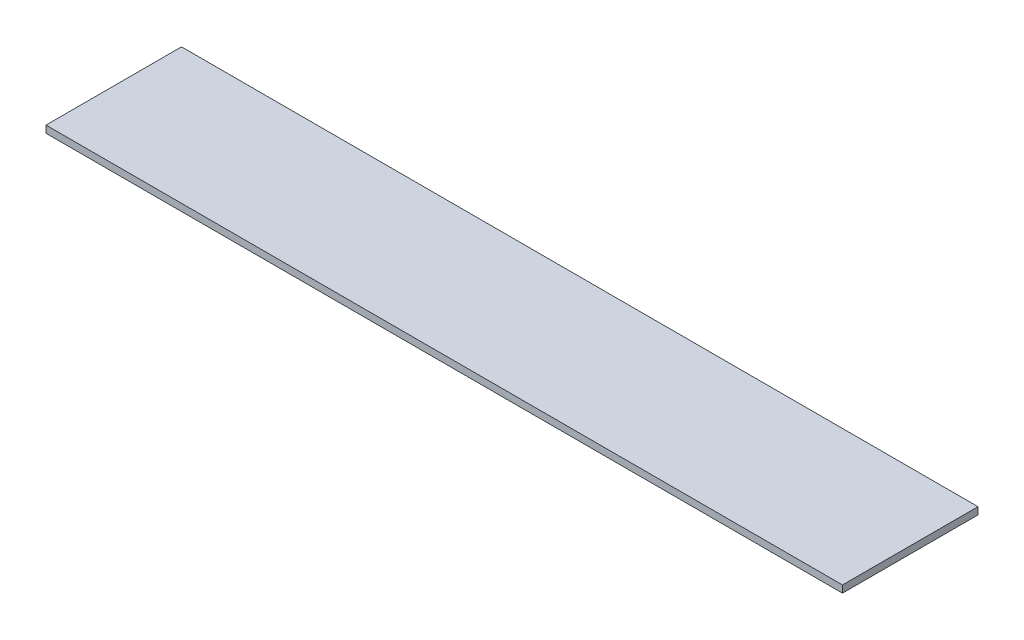
SolidWorks part; units mm, degrees
material "Pino"
ref_plane "Alzado" through (0, 0, 0) normal (0, 0, 1) x (1, 0, 0)
ref_plane "Planta" through (0, 0, 0) normal (0, 1, 0) x (1, 0, 0)
ref_plane "Vista lateral" through (0, 0, 0) normal (1, 0, 0) x (0, 0, -1)
sketch "Sketch1" plane through (0, 0, 0) normal (0, 1, 0) x (1, 0, 0)
  line L1 (-167.5, -28.5) -> (167.5, -28.5)
  line L2 (-167.5, -28.5) -> (-167.5, 28.5)
  line L3 (-167.5, 28.5) -> (167.5, 28.5)
  line L4 (167.5, -28.5) -> (167.5, 28.5)
  line L5 (-167.5, -28.5) -> (167.5, 28.5) construction
  line L6 (-167.5, 28.5) -> (167.5, -28.5) construction
  point P0 (0, 0)
  dimension "D1" = 335
  dimension "D2" = 57
extrude "Extrude1" add sketch "Sketch1" along normal blind 3
sketch "Sketch2" plane through (0, 3, 0) normal (0, 1, 0) x (1, 0, 0)
  circle A0 centre (0, -3) radius 11.25
  dimension "D1" = 22.5
  dimension "D2" = 3
extrude "Extrude2" [suppressed] cut sketch "Sketch2" against normal up to next
